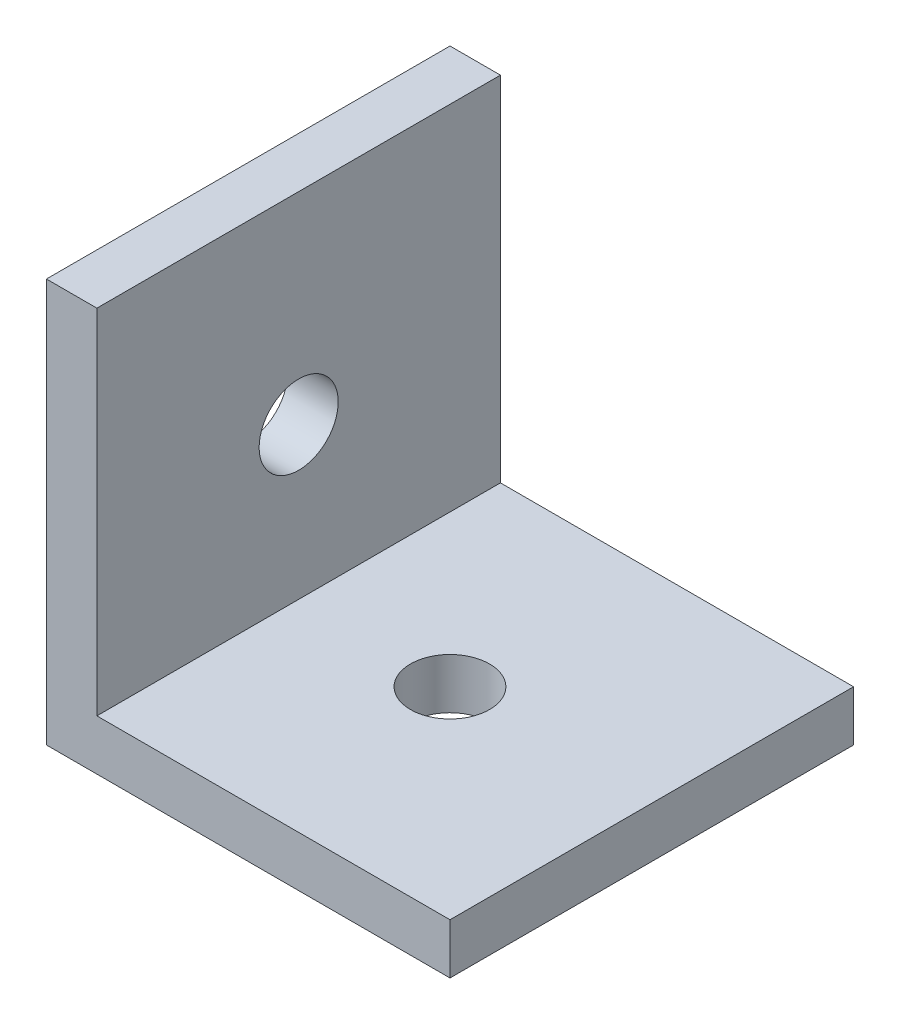
SolidWorks part; units mm, degrees
ref_plane "Front" through (0, 0, 0) normal (0, 0, 1) x (1, 0, 0)
ref_plane "Top" through (0, 0, 0) normal (0, 1, 0) x (1, 0, 0)
ref_plane "Right" through (0, 0, 0) normal (1, 0, 0) x (0, 0, -1)
sketch "Sketch1" plane through (0, 0, 0) normal (0, 0, 1) x (1, 0, 0)
  line L0 (0, 25.4) -> (0, 0)
  line L1 (0, 0) -> (25.4, 0)
  dimension "D1" = 25.4
extrude "Extrude-Thin1" add sketch "Sketch1" along normal mid plane 25.4 thin thin type one direction reverse wall 3.175
sketch "Sketch2" plane through (0, 3.175, 0) normal (0, 1, 0) x (1, 0, 0)
  line L0 (25.4, 0) -> (12.7, 0) construction
  line L1 (25.4, -12.7) -> (25.4, 12.7) construction
  circle A0 centre (12.7, 0) radius 2.4892
  dimension "D1" = 4.9784
  dimension "D2" = 12.7
extrude "Cut-Extrude1" cut sketch "Sketch2" against normal through all
ref_plane "Plane1" through (0, 0, 0) normal (0.7071, -0.7071, 0) x (-0.7071, -0.7071, 0)
mirror "Mirror1" about plane through (0, 0, 0) normal (0.7071, -0.7071, 0) of "Cut-Extrude1"
